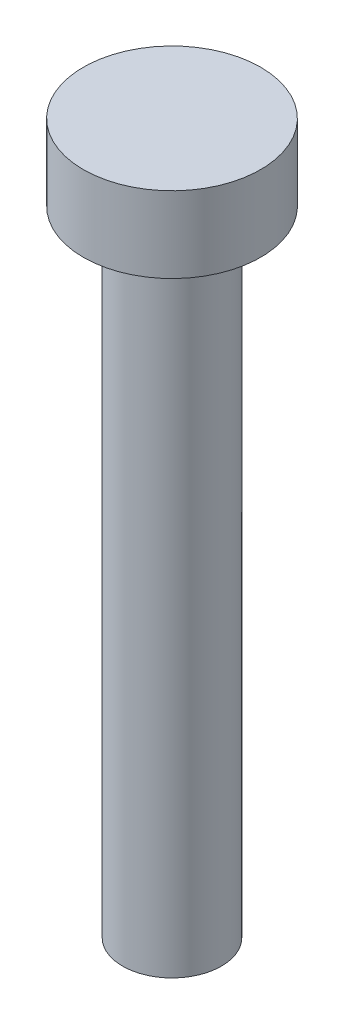
SolidWorks part; units mm, degrees
ref_plane "Front Plane" through (0, 0, 0) normal (0, 0, 1) x (1, 0, 0)
ref_plane "Top Plane" through (0, 0, 0) normal (0, 1, 0) x (1, 0, 0)
ref_plane "Right Plane" through (0, 0, 0) normal (1, 0, 0) x (0, 0, -1)
sketch "Sketch1" plane through (0, 0, 0) normal (0, 1, 0) x (1, 0, 0)
  circle A0 centre (0, 0) radius 3.5
  dimension "D1" = 7
extrude "Boss-Extrude1" add sketch "Sketch1" along normal blind 3
sketch "Sketch2" plane through (0, 0, 0) normal (0, -1, 0) x (1, 0, 0)
  circle A0 centre (0, 0) radius 1.95
  dimension "D1" = 3.9
extrude "Boss-Extrude2" add sketch "Sketch2" along normal blind 25
